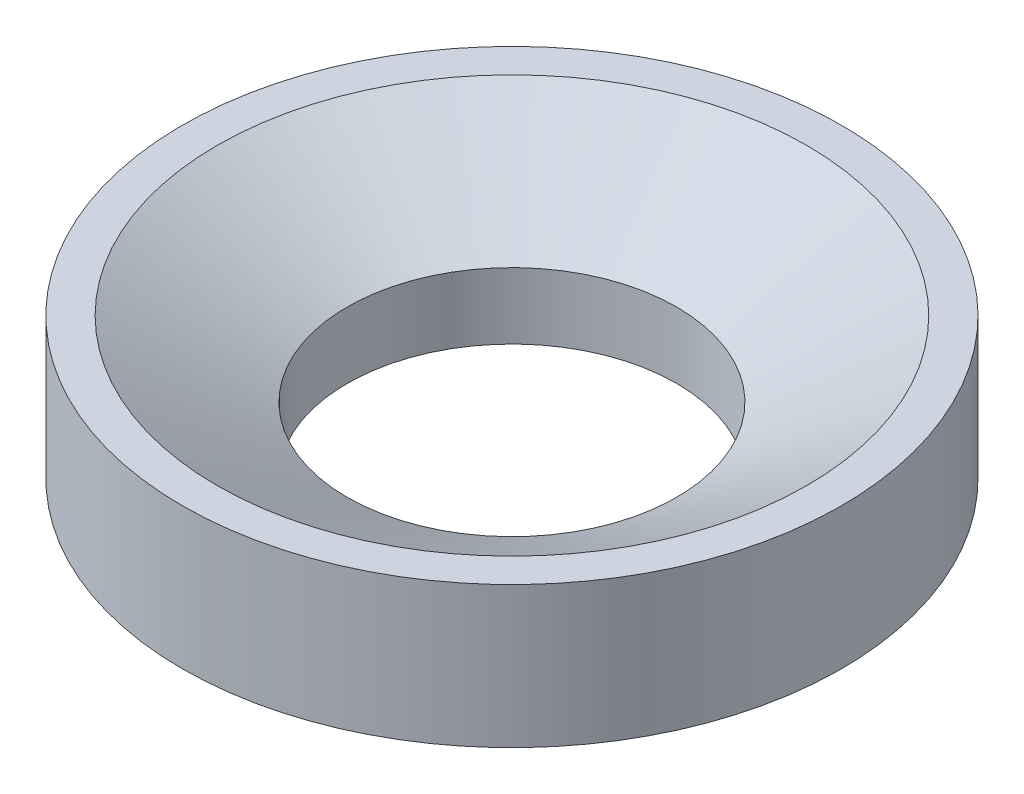
SolidWorks part; units mm, degrees
ref_plane "Front Plane" through (0, 0, 0) normal (0, 0, 1) x (1, 0, 0)
ref_plane "Top Plane" through (0, 0, 0) normal (0, 1, 0) x (1, 0, 0)
ref_plane "Right Plane" through (0, 0, 0) normal (1, 0, 0) x (0, 0, -1)
sketch "Sketch2" plane through (0, 0, 0) normal (0, 0, 1) x (1, 0, 0)
  line L5 (0, 44.6684) -> (0, -64.1085) construction
  line L8 (79.5076, 38.1) -> (88.9, 38.1)
  line L9 (44.45, 0) -> (88.9, 0)
  line L10 (88.9, 0) -> (88.9, 38.1)
  line L15 (44.45, 0) -> (44.45, 17.8595)
  line L16 (44.45, 17.8595) -> (79.5076, 38.1)
  line L17 (44.45, 17.8595) -> (92.1501, 17.8595) construction
  dimension "D1" = 44.45
  dimension "D2" = 44.45
  dimension "D3" = 38.1
  dimension "D4" = 30
revolve "Revolve1" add sketch "Sketch2" angle 360 about L5
